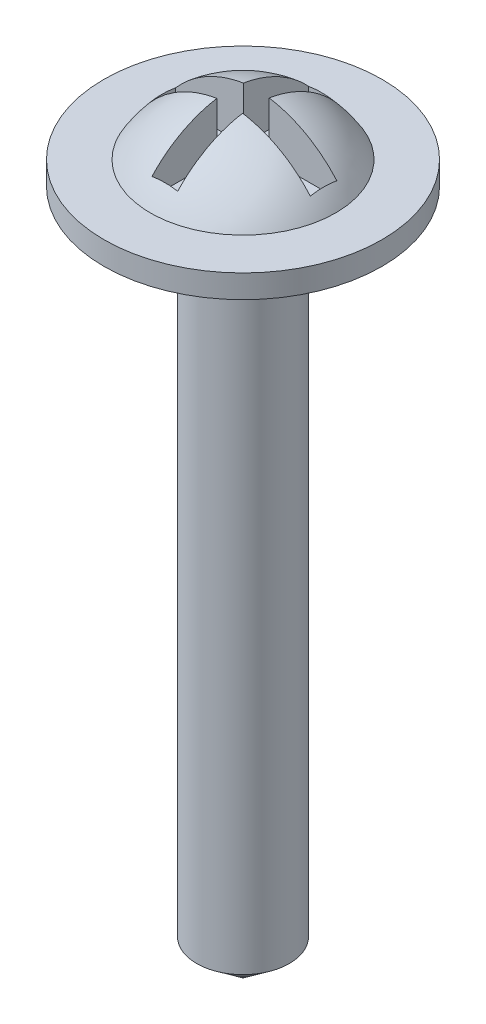
SolidWorks part; units mm, degrees
ref_plane "Front Plane" through (0, 0, 0) normal (0, 0, 1) x (1, 0, 0)
ref_plane "Top Plane" through (0, 0, 0) normal (0, 1, 0) x (1, 0, 0)
ref_plane "Right Plane" through (0, 0, 0) normal (1, 0, 0) x (0, 0, -1)
sketch "Sketch1" plane through (0, 0, 0) normal (1, 0, 0) x (0, 0, -1)
  line L0 (0, 0) -> (0, 16.5)
  line L1 (0, 0) -> (-1, 0.7694)
  line L2 (-1, 0.7694) -> (-1, 14.8)
  line L3 (-1, 14.8) -> (-3, 14.8)
  line L4 (-3, 14.8) -> (-3, 15.3)
  line L5 (-3, 15.3) -> (-2, 15.3)
  arc A0 (-2, 15.3) -> (0, 16.5) centre (0.1377, 14.0038) cw
  point P2 (-3, 15.05)
  dimension "D7" = 2.5
  dimension "D1" = 16.5
  dimension "D2" = 1
  dimension "D3" = 14.8
  dimension "D4" = 0.5
  dimension "D5" = 3
  dimension "D6" = 2
revolve "Revolve1" add sketch "Sketch1" angle 360 about L0
sketch "Sketch2" plane through (0, 15.3, 0) normal (0, 1, 0) x (1, 0, 0)
  line L1 (0.278, -1.687) -> (-0.278, -1.687)
  line L2 (0.278, -1.687) -> (0.278, -0.2866)
  line L3 (0.278, 1.687) -> (-0.278, 1.687)
  line L4 (-0.278, -1.687) -> (-0.278, -0.2866)
  line L5 (0.278, -1.687) -> (-0.278, 1.687) construction
  line L6 (0.278, 1.687) -> (-0.278, -1.687) construction
  line L7 (1.7393, -0.2866) -> (0.278, -0.2866)
  line L8 (1.7393, -0.2866) -> (1.7393, 0.2866)
  line L9 (1.7393, 0.2866) -> (0.278, 0.2866)
  line L10 (-1.7393, -0.2866) -> (-1.7393, 0.2866)
  line L11 (1.7393, -0.2866) -> (-1.7393, 0.2866) construction
  line L12 (1.7393, 0.2866) -> (-1.7393, -0.2866) construction
  line L13 (-0.278, -0.2866) -> (-1.7393, -0.2866)
  line L14 (-0.278, 0.2866) -> (-0.278, 1.687)
  line L15 (-0.278, 0.2866) -> (-1.7393, 0.2866)
  line L16 (0.278, 0.2866) -> (0.278, 1.687)
  point P0 (0, 0)
  point P6 (0, 0)
extrude "Cut-Extrude1" cut sketch "Sketch2" along normal blind 10
